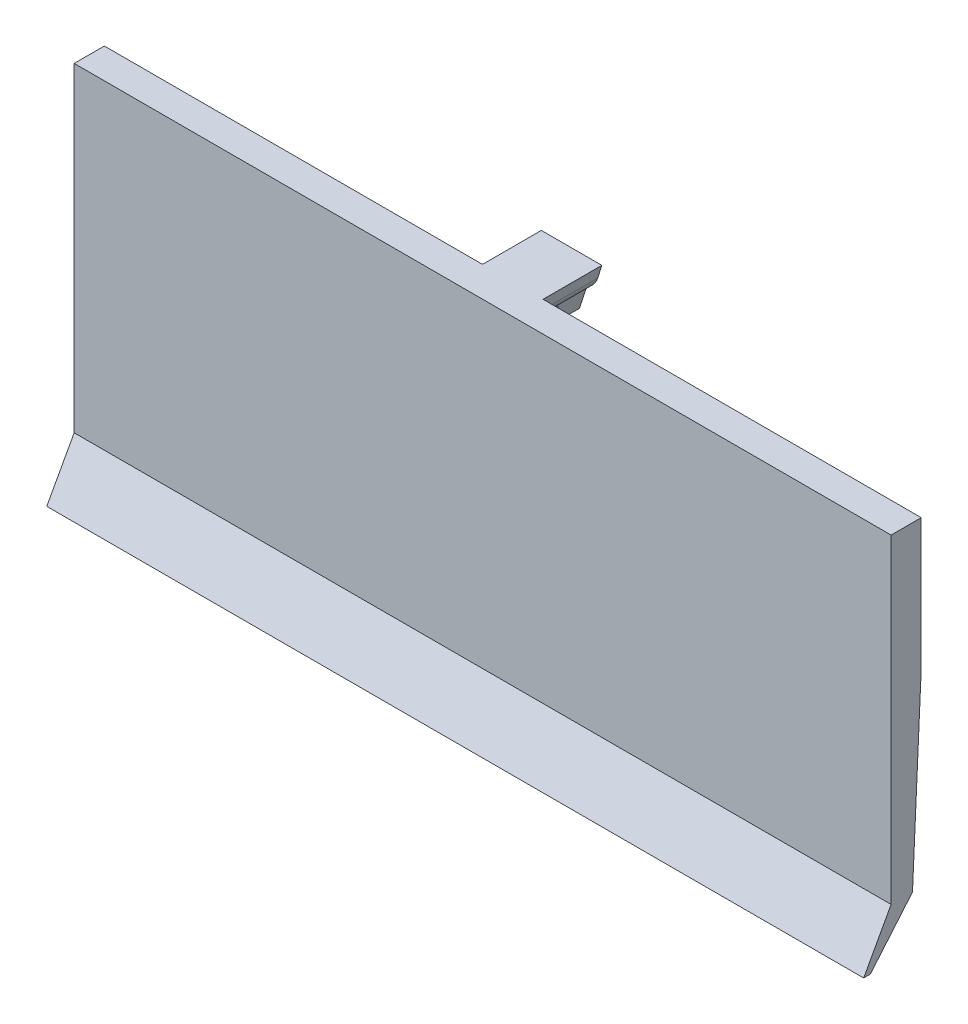
SolidWorks part; units mm, degrees
material "ABS"
ref_plane "前视基准面" through (0, 0, 0) normal (0, 0, 1) x (1, 0, 0)
ref_plane "上视基准面" through (0, 0, 0) normal (0, 1, 0) x (1, 0, 0)
ref_plane "右视基准面" through (0, 0, 0) normal (1, 0, 0) x (0, 0, -1)
sketch "草图1" plane through (0, 0, 0) normal (1, 0, 0) x (0, 0, -1)
  line L0 (0, 20.187) -> (0, -21.4602) construction
  line L4 (6.4964, -5.2349) -> (6.4964, -1.1913)
  line L11 (6.4964, 1.3881) -> (6.4964, -1.1913)
  line L12 (0, 13.2651) -> (0, 9.0243)
  line L14 (1.9928, 13.4349) -> (1.9928, 8.9664)
  line L16 (0, 13.2651) -> (0, 15.5311)
  line L17 (0, 15.5311) -> (1.9928, 15.5311)
  line L18 (1.9928, 15.5311) -> (1.9928, 13.4349)
  line L19 (0, 9.0243) -> (0, 5.5311)
  line L20 (0, 5.5311) -> (1.076, 5.5311)
  line L21 (1.076, 5.5311) -> (2.1271, 3.7449)
  line L22 (2.1271, 3.7449) -> (2.1271, 3.316)
  line L23 (2.1271, 3.316) -> (3.852, 3.316)
  line L24 (3.852, 3.316) -> (3.852, -5.2349)
  line L25 (3.852, -5.2349) -> (6.4964, -5.2349)
  line L26 (8.352, -5.2349) -> (3.852, -5.2349) construction
  line L27 (1.9928, 8.9664) -> (1.9928, 6.9076)
  line L28 (2.4921, 5.9266) -> (6.4964, 3.4009)
  line L29 (6.4964, 3.4009) -> (6.4964, 1.3881)
  line L30 (1.9928, 6.9076) -> (2.4921, 5.9266)
  dimension "D1" = 10
  dimension "D3" = 2
extrude "凸台-拉伸1" add sketch "草图1" along normal mid plane 54 contours L4 L11 L29 L28 L30 L27 L14 L18 L17 L16 L12 L19 L20 L21 L22 L23 L24 L25
sketch "草图2" plane through (0, 0, -6.4964) normal (0, 0, -1) x (-1, 0, 0)
  line L0 (0, 8.1951) -> (0, -10.3459) construction
  line L1 (-4.5, -5.7349) -> (-4.5, -1.7349)
  line L3 (-4.5, -1.7349) -> (4.5, -1.7349)
  line L4 (4.5, -1.7349) -> (4.5, -5.7349)
  line L5 (4.5, -5.7349) -> (-4.5, -5.7349)
  dimension "D1" = 9
  dimension "D2" = 4.5
extrude "切除-拉伸1" cut sketch "草图2" against normal blind 4
sketch "草图3" plane through (0, 0, -6.4964) normal (0, 0, -1) x (-1, 0, 0)
  line L1 (4.5, -1.7349) -> (-4.5, -1.7349)
  line L2 (4.5, -1.7349) -> (4.5, 1.3032)
  line L3 (4.5, 1.3032) -> (-4.5, 1.3032)
  line L4 (-4.5, -1.7349) -> (-4.5, 1.3032)
extrude "凸台-拉伸2" add sketch "草图3" along normal blind 3
sketch "草图4" plane through (0, -1.7349, 0) normal (0, -1, 0) x (1, 0, 0)
  circle A0 centre (0, -6.102) radius 1.5
extrude "切除-拉伸2" cut sketch "草图4" against normal blind 9
sketch "草图6" plane through (0, 0, 0) normal (1, 0, 0) x (0, 0, -1)
  line L0 (1.8802, 15.5311) -> (5.8802, 15.5311)
  line L1 (5.8802, 15.5311) -> (5.8802, 12.3311)
  line L2 (5.8802, 12.3311) -> (4.0802, 12.3311)
  line L3 (4.0802, 12.3311) -> (4.0802, 13.5311)
  line L4 (4.0802, 13.5311) -> (2.0593, 13.5311)
  line L7 (2.0593, 13.5311) -> (1.8802, 13.5311)
  line L8 (1.8802, 13.5311) -> (1.8802, 15.5311)
  dimension "D1" = 2
  dimension "D2" = 4
  dimension "D3" = 1.8
  dimension "D4" = 1.2
extrude "凸台-拉伸3" add sketch "草图6" along normal mid plane 4 contours L0 L1 L2 L3 L4 L7 L8
sketch "草图7" plane through (0, 0, -5.8802) normal (0, 0, -1) x (-1, 0, 0)
  line L0 (-2, 15.5311) -> (-1.7231, 14.6594)
  line L1 (-1, 13.8311) -> (-0.5234, 12.3311)
  line L2 (-2, 12.3311) -> (2, 12.3311) construction
  line L3 (0, 17.1262) -> (0, 11.4925) construction
  line L5 (-2, 15.5311) -> (2, 15.5311) construction
  line L8 (2, 15.5311) -> (1.7231, 14.6594)
  line L9 (1, 13.8311) -> (0.5234, 12.3311)
  line L10 (-2, 15.5311) -> (-2, 12.3311)
  line L11 (-2, 12.3311) -> (-0.5234, 12.3311)
  line L12 (0.5234, 12.3311) -> (2, 12.3311)
  line L13 (2, 12.3311) -> (2, 15.5311)
  arc A0 (-1.7231, 14.6594) -> (-1, 13.8311) centre (-0.4086, 15.0771) ccw
  arc A1 (1.7231, 14.6594) -> (1, 13.8311) centre (0.4086, 15.0771) cw
  point P13 (0, 15.5311)
  point P20 (0, 12.3311)
  line M5 (2, 12.3311) -> (2, 15.5311)
  line M8 (-2, 12.3311) -> (2, 12.3311)
  dimension "D1" = 1
  dimension "D2" = 1.7
extrude "切除-拉伸8" cut sketch "草图7" against normal up to surface (3.8875 mm away) contours L8 A1 L9 M8 M5 | A0 L1 L11 L10 L0 up to face at (0, 12.8752, -1.9928)
sketch "草图8" plane through (-27, 0, 0) normal (-1, 0, 0) x (0, 0, 1)
  line L1 (-12.403, 5.2501) -> (-3.7923, 5.2501)
  line L2 (-12.403, 5.2501) -> (-12.403, -7.998)
  line L3 (-12.403, -7.998) -> (-3.7923, -7.998)
  line L4 (-3.7923, 5.2501) -> (-3.7923, -7.998)
extrude "切除-拉伸9" cut sketch "草图8" against normal up to surface (54 mm away) up to face at (27, 4.8556, -2.7087)
sketch "草图9" plane through (-27, 0, 0) normal (-1, 0, 0) x (0, 0, 1)
  line L0 (-2.2152, 3.316) -> (-2.1271, 3.316)
  line L1 (-2.2152, -5.614) -> (-3.7923, -5.614)
  line L2 (-2.2152, -5.614) -> (-2.2152, 0.3919)
  line L3 (-2.2152, 3.316) -> (-3.7923, 3.316)
  line L4 (-3.7923, -5.614) -> (-3.7923, 3.316)
  line L5 (-2.1271, 3.316) -> (-2.2152, 0.3919)
extrude "凸台-拉伸4" add sketch "草图9" against normal up to surface (54 mm away) up to face at (27, 7.0442, -1.9392)
sketch "草图10" plane through (0, 0, -3.7923) normal (0, 0, -1) x (-1, 0, 0)
  line L0 (0, 11.0087) -> (0, -9.6116) construction
  line L1 (3, -7.1031) -> (-3, -7.1031)
  line L2 (3, -7.1031) -> (3, 7.6995)
  line L3 (3, 7.6995) -> (-3, 7.6995)
  line L4 (-3, -7.1031) -> (-3, 7.6995)
  line L5 (3, -7.1031) -> (-3, 7.6995) construction
  line L6 (3, 7.6995) -> (-3, -7.1031) construction
  point P0 (0, 0.2982)
  dimension "D1" = 6
sketch "草图12" plane through (0, 0, -2.2152) normal (0, 0, 1) x (1, 0, 0)
  line L1 (-27, -5.614) -> (-3, -5.614)
  line L2 (-27, -5.614) -> (-27, 0.3919)
  line L3 (-27, 0.3919) -> (-3, 0.3919)
  line L4 (-3, -5.614) -> (-3, 0.3919)
  line L9 (3, 0.4185) -> (27, 0.4185)
  line L10 (3, 0.4185) -> (3, -5.614)
  line L11 (3, -5.614) -> (27, -5.614)
  line L12 (27, 0.4185) -> (27, -5.614)
extrude "凸台-拉伸6" add sketch "草图12" along normal up to surface (2.2152 mm away) up to face at (0, 10.5311, 0)
sketch "草图14" plane through (27, 0, 0) normal (1, 0, 0) x (0, 0, -1)
  line L0 (0, 5.5311) -> (0, 0.203)
  line L1 (0, 0.4185) -> (0, -5.614) construction
  line L2 (0, 0.203) -> (0, -5.614)
  line L3 (0, -5.614) -> (-1.8116, -8.9194)
  line L4 (-1.8116, -8.9194) -> (-1.3701, -8.9194)
  line L5 (-1.3701, -8.9194) -> (1.4141, -5.614)
  line L6 (3.7923, -5.614) -> (0, -5.614) construction
  line L7 (1.4141, -5.614) -> (1.9928, 6.9076)
  line L8 (1.9928, 6.9076) -> (0, 6.9076)
  line L9 (0, 5.5311) -> (0, 15.5311) construction
  line L10 (0, 6.9076) -> (0, 5.5311)
extrude "凸台-拉伸7" add sketch "草图14" against normal up to surface (54 mm away) up to face at (-27, 4.3601, -1.6621)
sketch "草图15" plane through (27, 0, 0) normal (1, 0, 0) x (0, 0, -1)
  line L0 (1.9928, 6.9076) -> (1.4141, -5.614)
  line L1 (1.4141, -5.614) -> (3.7923, -5.614)
  line L2 (3.7923, -5.614) -> (3.7923, 5.1065)
  line L3 (3.7923, -5.614) -> (3.7923, 5.1065) construction
  line L4 (2.4921, 5.9266) -> (3.7923, 5.1065) construction
  line L5 (3.7923, 5.1065) -> (1.9928, 6.9076)
extrude "切除-拉伸11" cut sketch "草图15" against normal up to surface (54 mm away)
